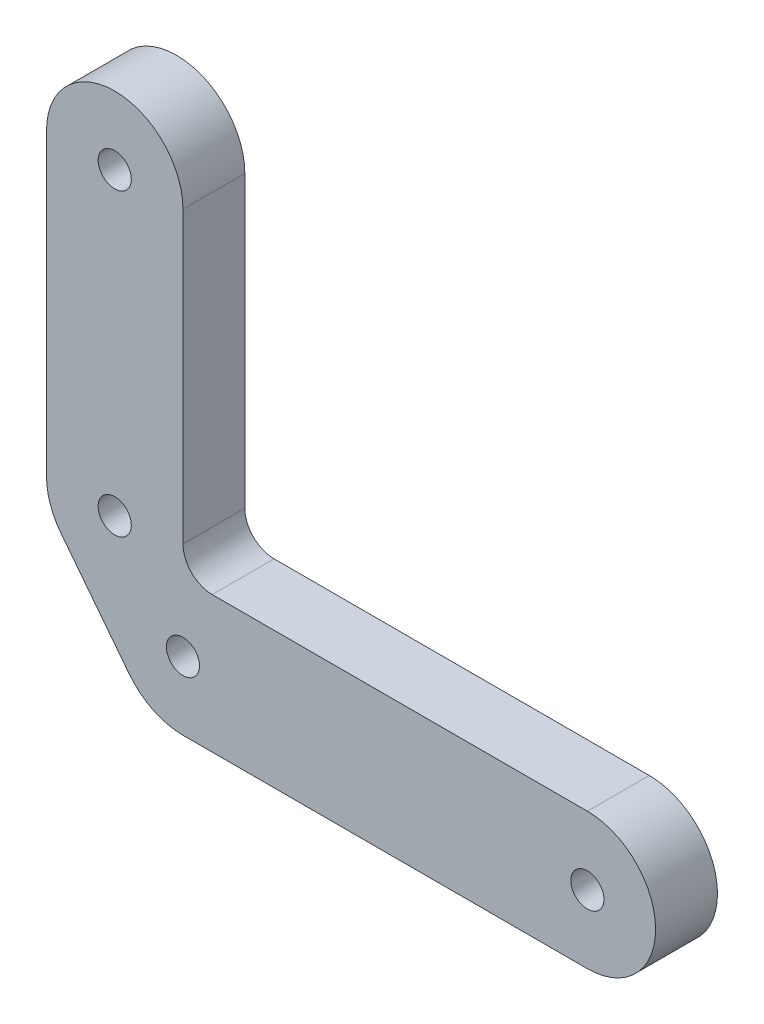
SolidWorks part; units mm, degrees
material "6061-T6 (SS)"
ref_plane "Front" through (0, 0, 0) normal (0, 0, 1) x (1, 0, 0)
ref_plane "Top" through (0, 0, 0) normal (0, 1, 0) x (1, 0, 0)
ref_plane "Right" through (0, 0, 0) normal (1, 0, 0) x (0, 0, -1)
sketch "Sketch2" plane through (0, 0, 0) normal (0, 0, 1) x (1, 0, 0)
  line L0 (-14, 39.75) -> (-14, 9)
  line L1 (-12.5255, 4.7024) -> (-5.5255, -4.2976)
  line L2 (0, -7) -> (41.5, -7)
  line L3 (41.5, 7) -> (0, 7)
  line L4 (0, 7) -> (0, 39.75)
  line L5 (41.5, 7) -> (41.5, -7) construction
  circle A0 centre (41.5, 0) radius 7 construction
  circle A1 centre (0, 0) radius 7 construction
  circle A2 centre (-7, 9) radius 7 construction
  circle A3 centre (-7, 39.75) radius 7 construction
  arc A4 (-14, 39.75) -> (0, 39.75) centre (-7, 39.75) cw
  arc A5 (-14, 9) -> (-12.5255, 4.7024) centre (-7, 9) ccw
  arc A6 (-5.5255, -4.2976) -> (0, -7) centre (0, 0) ccw
  arc A7 (41.5, -7) -> (41.5, 7) centre (41.5, 0) ccw
  dimension "D5" = 14
  dimension "D1" = 41.5
  dimension "D2" = 30.75
  dimension "D3" = 9
extrude "Boss-Extrude1" add sketch "Sketch2" along normal blind 6.35
fillet "Fillet1" radius 3 1 edges at (0, 7, 3.175)
hole_wizard "M3 Clearance Hole1" positions "Sketch4" profile "Sketch3" hole size "M3" standard "ISO" end condition through all
sketch "Sketch4" plane through (0, 0, 6.35) normal (0, 0, 1) x (1, 0, 0)
  point P0 (-7, 39.75)
  point P3 (-7, 9)
  point P6 (0, 0)
  point P9 (41.5, 0)
sketch "Sketch3" plane through (-7, 39.75, 6.35) normal (1, 0, 0) x (0, -1, 0)
  line L0 (0, 0) -> (0, 6.35)
  line L1 (0, 6.35) -> (1.7, 6.35)
  line L2 (1.7, 6.35) -> (1.7, 0)
  line L5 (1.7, 0) -> (0, 0)
  line L11 (0, -6.35) -> (0, 107.95) construction
  dimension "Thru Hole Dia." = 3.4
  dimension "Thru Hole Depth" = 6.35
